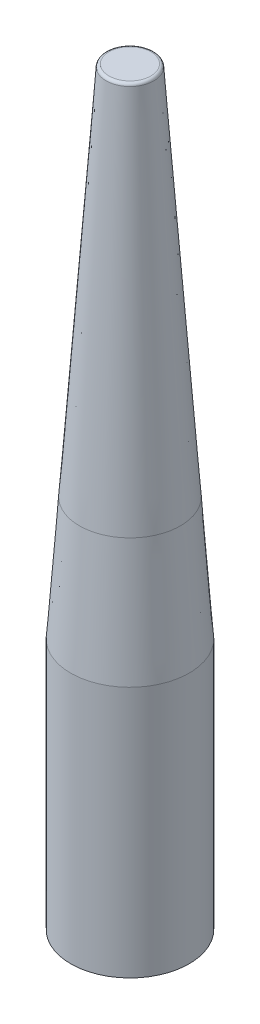
SolidWorks part; units mm, degrees
ref_plane "Front Plane" through (0, 0, 0) normal (0, 0, 1) x (1, 0, 0)
ref_plane "Top Plane" through (0, 0, 0) normal (0, 1, 0) x (1, 0, 0)
ref_plane "Right Plane" through (0, 0, 0) normal (1, 0, 0) x (0, 0, -1)
sketch "Sketch1" plane through (0, 0, 0) normal (0, 0, 1) x (1, 0, 0)
  line L0 (27.051, 0) -> (27.051, 107.95)
  line L1 (27.051, 107.95) -> (11.811, 321.31)
  line L2 (11.811, 321.31) -> (0, 321.31)
  line L3 (0, 321.31) -> (0, 0)
  line L4 (0, 0) -> (27.051, 0)
  line L5 (11.811, 321.31) -> (0, 486.664)
  line L6 (0, 486.664) -> (0, 321.31)
  line L7 (25.4, 0) -> (25.4, 107.8911)
  line L8 (25.4, 107.8911) -> (10.1558, 321.31)
  line L9 (25.4, 107.8911) -> (10.1642, 321.1924) construction
  dimension "D1" = 107.95
  dimension "D2" = 11.811
  dimension "D3" = 378.714
  dimension "D4" = 27.051
  dimension "D5" = 1.651
revolve "Revolve1" add sketch "Sketch1" angle 360 about L3
fillet "Fillet1" radius 1.27 1 edges at (-10.1558, 321.31, 0)
ref_plane "Plane1" through (0, 160.655, 0) normal (0, 1, 0) x (1, 0, 0)
split "Split1" trim tools "Plane1" bodies to split 101 resulting bodies 102 103
sketch "Sketch4" plane through (0, 160.655, 0) normal (0, 1, 0) x (1, 0, 0)
  circle A0 centre (0, 0) radius 10.16
  dimension "D1" = 20.32
extrude "Boss-Extrude1" add sketch "Sketch4" along normal blind 12.7
sketch "Sketch5" plane through (0, 160.655, 0) normal (0, -1, 0) x (1, 0, 0)
  circle A0 centre (0, 0) radius 10.2235
  dimension "D1" = 20.447
extrude "Cut-Extrude1" cut sketch "Sketch5" against normal blind 13.97
chamfer "Chamfer1" distance 1.27 angle 45 1 edges at (10.2235, 160.655, 0)
